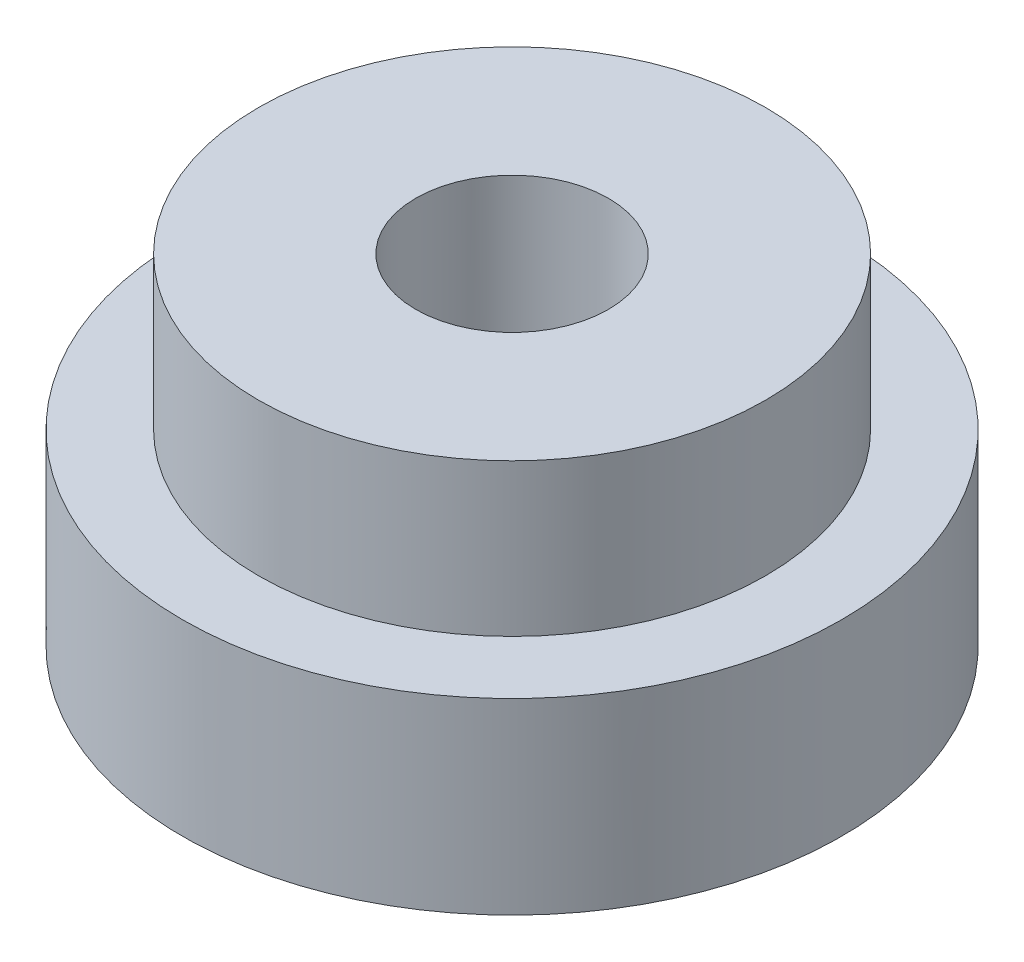
SolidWorks part; units mm, degrees
ref_plane "Alzado" through (0, 0, 0) normal (0, 0, 1) x (1, 0, 0)
ref_plane "Planta" through (0, 0, 0) normal (0, 1, 0) x (1, 0, 0)
ref_plane "Vista lateral" through (0, 0, 0) normal (1, 0, 0) x (0, 0, -1)
sketch "Croquis1" plane through (0, 0, 0) normal (0, 1, 0) x (1, 0, 0)
  circle A0 centre (0, 0) radius 6.5
  dimension "D1" = 13
extrude "Saliente-Extruir1" add sketch "Croquis1" along normal blind 1.2
sketch "Croquis2" plane through (0, 1.2, 0) normal (0, 1, 0) x (1, 0, 0)
  circle A0 centre (0, 0) radius 5
  dimension "D1" = 10
extrude "Saliente-Extruir2" add sketch "Croquis2" along normal blind 3
sketch "Croquis3" plane through (0, 4.2, 0) normal (0, 1, 0) x (1, 0, 0)
  circle A0 centre (0, 0) radius 1.8
  dimension "D1" = 3.6
extrude "Cortar-Extruir1" cut sketch "Croquis3" against normal blind 3
sketch "Croquis4" plane through (0, 0, 0) normal (0, -1, 0) x (1, 0, 0)
  circle A0 centre (0, 0) radius 1.9
  dimension "D1" = 3.8
extrude "Cortar-Extruir2" cut sketch "Croquis4" against normal up to next
sketch "Croquis5" plane through (0, 0, 0) normal (0, -1, 0) x (1, 0, 0)
  circle A0 centre (0, 0) radius 6.5
  circle A3 centre (0, 0) radius 6.5 construction
extrude "Saliente-Extruir3" add sketch "Croquis5" along normal blind 2.5
sketch "Croquis6" plane through (0, -2.5, 0) normal (0, -1, 0) x (1, 0, 0)
  line L1 (-3.3007, 1.2282) -> (-2.714, -2.2444)
  line L2 (-2.714, -2.2444) -> (0.5867, -3.4726)
  line L3 (0.5867, -3.4726) -> (3.3007, -1.2282)
  line L4 (3.3007, -1.2282) -> (2.714, 2.2444)
  line L5 (2.714, 2.2444) -> (-0.5867, 3.4726)
  line L6 (-0.5867, 3.4726) -> (-3.3007, 1.2282)
  circle A0 centre (0, 0) radius 3.05 construction
  dimension "D1" = 6.1
extrude "Cortar-Extruir3" cut sketch "Croquis6" against normal blind 2.5
